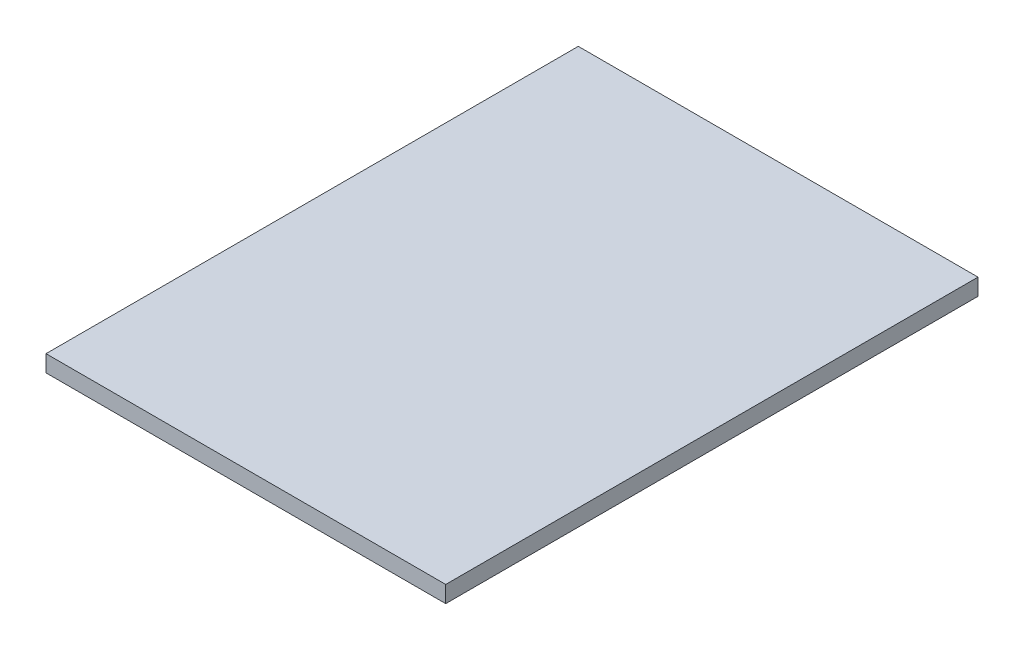
SolidWorks part; units mm, degrees
ref_plane "Front Plane" through (0, 0, 0) normal (0, 0, 1) x (1, 0, 0)
ref_plane "Top Plane" through (0, 0, 0) normal (0, 1, 0) x (1, 0, 0)
ref_plane "Right Plane" through (0, 0, 0) normal (1, 0, 0) x (0, 0, -1)
sketch "Sketch3" plane through (0, 0, 0) normal (0, 1, 0) x (1, 0, 0)
  line L1 (0, 0) -> (152.4, 0)
  line L2 (0, 0) -> (0, 202.946)
  line L3 (0, 202.946) -> (152.4, 202.946)
  line L4 (152.4, 0) -> (152.4, 202.946)
  dimension "D1" = 152.4
  dimension "D2" = 202.946
extrude "Boss-Extrude1" add sketch "Sketch3" along normal blind 6.35
